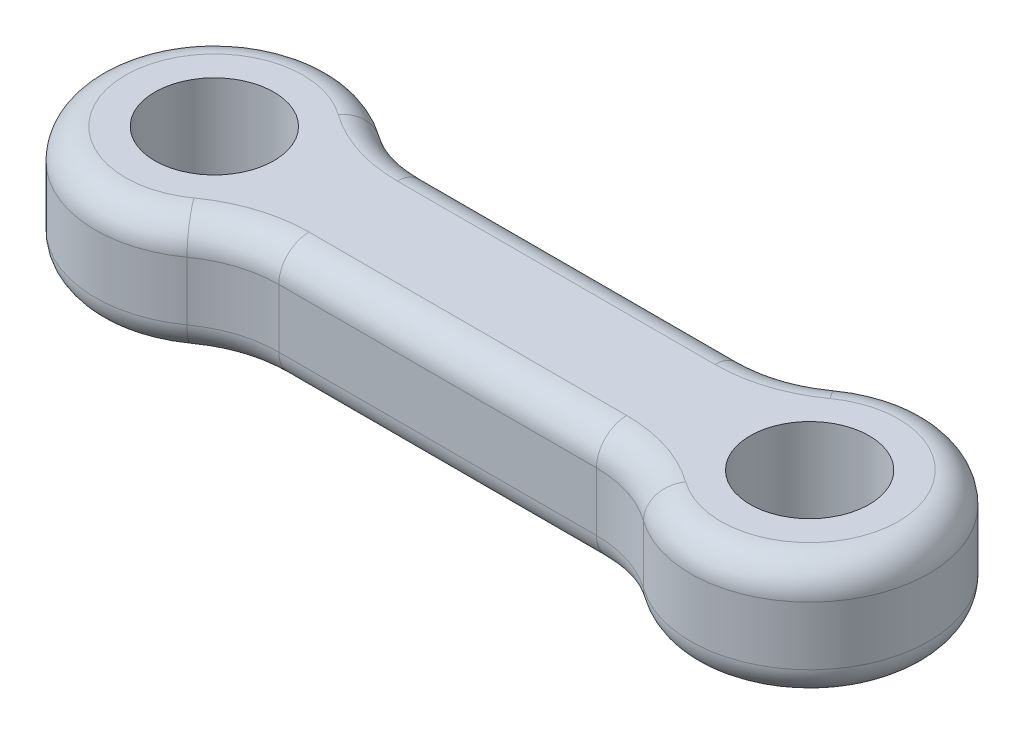
SolidWorks part; units mm, degrees
ref_plane "Front Plane" through (0, 0, 0) normal (0, 0, 1) x (1, 0, 0)
ref_plane "Top Plane" through (0, 0, 0) normal (0, 1, 0) x (1, 0, 0)
ref_plane "Right Plane" through (0, 0, 0) normal (1, 0, 0) x (0, 0, -1)
sketch "Sketch1" plane through (0, 0, 0) normal (0, 1, 0) x (1, 0, 0)
  line L0 (-12.5, 0) -> (12.5, 0) construction
  line L1 (-0.8408, -6.25) -> (25.8408, -6.25)
  line L2 (-0.8408, 6.25) -> (25.8408, 6.25)
  line L3 (-6.6704, -8.125) -> (-6.6704, 8.125) construction
  line L4 (-0.8408, -6.25) -> (-0.8408, 6.25) construction
  line L5 (12.5, -6.25) -> (12.5, 6.25) construction
  arc A0 (-6.6704, 8.125) -> (-6.6704, -8.125) centre (-12.5, 0) ccw
  arc A1 (-6.6704, -8.125) -> (-0.8408, -6.25) centre (-0.8408, -16.25) cw
  arc A2 (-6.6704, 8.125) -> (-0.8408, 6.25) centre (-0.8408, 16.25) ccw
  circle A3 centre (-12.5, 0) radius 5
  circle A4 centre (37.5, 0) radius 5
  arc A5 (31.6704, -8.125) -> (25.8408, -6.25) centre (25.8408, -16.25) ccw
  arc A6 (31.6704, 8.125) -> (31.6704, -8.125) centre (37.5, 0) cw
  arc A7 (31.6704, 8.125) -> (25.8408, 6.25) centre (25.8408, 16.25) cw
  dimension "D3" = 10
  dimension "D4" = 12.5
  dimension "D5" = 10
  dimension "D2" = 10
  dimension "D1" = 25
extrude "Boss-Extrude1" add sketch "Sketch1" along normal blind 10
fillet "Fillet1" radius 2.54 16 edges at (-22.5, 0, 0) (-3.9026, 0, 6.7303) (12.5, 0, 6.25) (28.9026, 0, 6.7303) (47.5, 0, 0) (28.9026, 0, -6.7303) (12.5, 0, -6.25) (-3.9026, 0, -6.7303) (12.5, 10, -6.25) (28.9026, 10, -6.7303) (47.5, 10, 0) (28.9026, 10, 6.7303) (12.5, 10, 6.25) (-3.9026, 10, 6.7303) (-22.5, 10, 0) (-3.9026, 10, -6.7303)
scale "Scale1" scale about centroid uniform scaling yes scale factor 0.66
